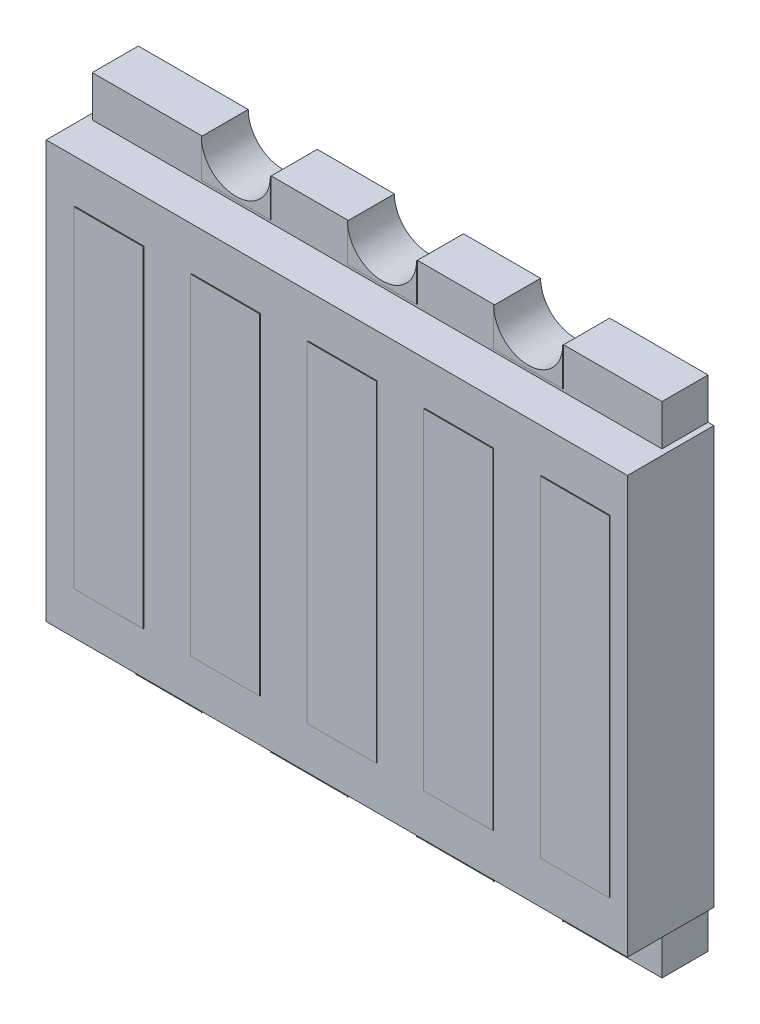
SolidWorks part; units mm, degrees
ref_plane "Front Plane" through (0, 0, 0) normal (0, 0, 1) x (1, 0, 0)
ref_plane "Top Plane" through (0, 0, 0) normal (0, 1, 0) x (1, 0, 0)
ref_plane "Right Plane" through (0, 0, 0) normal (1, 0, 0) x (0, 0, -1)
sketch "Sketch1" plane through (0, 0, 0) normal (0, 0, 1) x (1, 0, 0)
  line L1 (0, 0) -> (19.8, 0)
  line L2 (0, 0) -> (0, 17.35)
  line L3 (0, 17.35) -> (19.8, 17.35)
  line L4 (19.8, 0) -> (19.8, 17.35)
  dimension "D1" = 19.8
  dimension "D2" = 17.35
extrude "Boss-Extrude1" add sketch "Sketch1" along normal blind 1.6 contours L2 L3 L4 L1
sketch "Sketch3" plane through (0, 0, 0) normal (0, 0, 1) x (1, 0, 0)
  line L0 (9.9, 0) -> (11.3, 0)
  line L2 (0, 0) -> (19.8, 0) construction
  line L4 (9.9, 0) -> (8.9, 0)
  line L9 (15.18, 0) -> (16.38, 0)
  line L10 (5.02, 0) -> (3.82, 0)
  line L11 (5.02, 0) -> (6.22, 0)
  line L13 (13.98, 0) -> (15.18, 0)
  arc A0 (8.9, 0) -> (11.3, 0) centre (10.1, 0) cw
  arc A1 (3.82, 0) -> (6.22, 0) centre (5.02, 0) cw
  arc A2 (13.98, 0) -> (16.38, 0) centre (15.18, 0) cw
extrude "Cut-Extrude2" cut sketch "Sketch3" against normal blind 1.6 and the other way through all contours A0 L4 L0 | A2 L13 L9 | A1 L10 L11
ref_plane "Plane1" through (0, 8.675, 0) normal (0, 1, 0) x (1, 0, 0)
mirror "Mirror1" about plane through (0, 8.675, 0) normal (0, 1, 0) of "Cut-Extrude2"
sketch "Sketch4" plane through (0, 0, 0) normal (0, 0, 1) x (1, 0, 0)
  line L1 (19.8, 1.425) -> (20, 1.425)
  line L2 (0, 15.925) -> (-0.2, 15.925)
  line L3 (0, 0) -> (0, 17.35) construction
  line L4 (19.8, 0) -> (19.8, 17.35) construction
  line L6 (-0.2, 15.925) -> (20, 15.925)
  line L7 (-0.2, 15.925) -> (-0.2, 1.425)
  line L9 (-0.2, 1.425) -> (20, 1.425)
  line L10 (20, 15.925) -> (20, 1.425)
extrude "Boss-Extrude2" add sketch "Sketch4" along normal blind 3 contours L10 L6 L2 L7 L9 L1
sketch "Sketch6" plane through (0, 0, 3) normal (0, 0, 1) x (1, 0, 0)
  line L0 (1.5222, 0) -> (0.0972, 1.425)
  line L1 (0, 0) -> (3.82, 0) construction
  line L2 (0, 1.425) -> (19.8, 1.425) construction
  line L3 (0, 1.425) -> (0.0972, 1.425)
  line L4 (0, 1.425) -> (0, 0)
  line L5 (0, 0) -> (1.5222, 0)
extrude "Cut-Extrude3" cut sketch "Sketch6" against normal blind 3
sketch "Sketch7" plane through (0, 0, 1.6) normal (0, 0, 1) x (1, 0, 0)
  line L0 (3.82, 0) -> (3.82, 1.2)
  line L1 (3.82, 1.3125) -> (3.82, 1.2)
  line L2 (6.22, 1.2) -> (6.22, 0)
  line L3 (8.9, 0) -> (8.9, 1.2)
  line L4 (13.98, 1.2) -> (13.98, 1.3125)
  line L5 (11.3, 1.2) -> (11.3, 0)
  line L6 (13.98, 0) -> (13.98, 1.2)
  line L8 (16.38, 1.2) -> (16.38, 0)
  line L10 (3.82, 1.3125) -> (6.22, 1.3125)
  line L11 (6.22, 1.3125) -> (6.22, 1.2)
  line L12 (8.9, 1.2) -> (8.9, 1.3125)
  line L13 (8.9, 1.3125) -> (11.3, 1.3125)
  line L14 (11.3, 1.3125) -> (11.3, 1.2)
  line L15 (13.98, 1.3125) -> (16.38, 1.3125)
  line L16 (16.38, 1.3125) -> (16.38, 1.2)
  arc A0 (6.22, 0) -> (3.82, 0) centre (5.02, 0) ccw construction
  arc A1 (3.82, 0) -> (6.22, 0) centre (5.02, 0) cw
  arc A2 (16.38, 0) -> (13.98, 0) centre (15.18, 0) ccw construction
  arc A3 (8.9, 0) -> (11.3, 0) centre (10.1, 0) cw
  arc A4 (13.98, 0) -> (16.38, 0) centre (15.18, 0) cw
extrude "Boss-Extrude7" add sketch "Sketch7" along normal blind 0.03 separate body
mirror "Mirror2" about plane through (0, 8.675, 0) normal (0, 1, 0) of "Boss-Extrude7"
sketch "Sketch8" plane through (0, 0, 0) normal (0, 0, 1) x (1, 0, 0)
  line L7 (8.9, 14.425) -> (11.3, 14.425)
  line L8 (8.9, 14.425) -> (8.9, 2.925)
  line L9 (8.9, 2.925) -> (11.3, 2.925)
  line L10 (11.3, 14.425) -> (11.3, 2.925)
extrude "Boss-Extrude8" add sketch "Sketch8" along normal blind 3.03
pattern_linear "LPattern1" count 3 spacing 4.05 along (1, 0, 0) count 3 spacing 4.05 along (-1, 0, 0) of "Boss-Extrude8"
